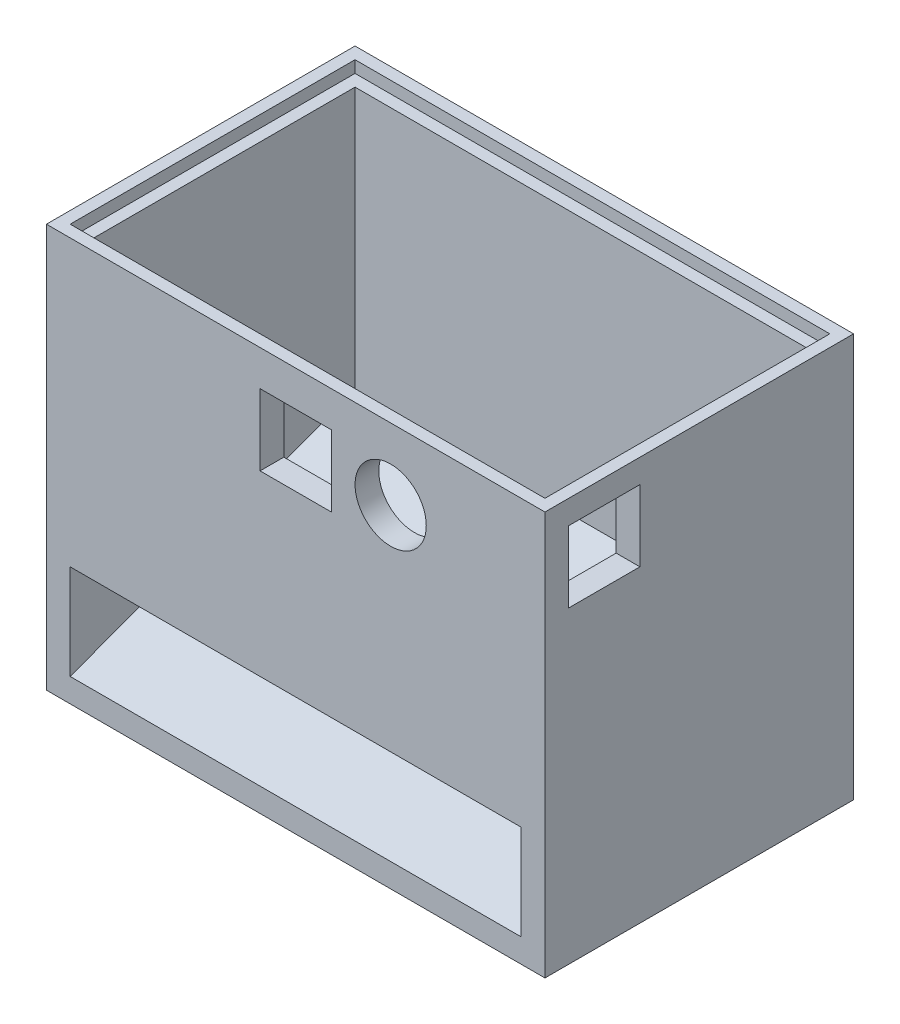
SolidWorks part; units mm, degrees
ref_plane "Front Plane" through (0, 0, 0) normal (0, 0, 1) x (1, 0, 0)
ref_plane "Top Plane" through (0, 0, 0) normal (0, 1, 0) x (1, 0, 0)
ref_plane "Right Plane" through (0, 0, 0) normal (1, 0, 0) x (0, 0, -1)
sketch "Sketch1" plane through (0, 0, 0) normal (0, 1, 0) x (1, 0, 0)
  line L1 (-52.5, -32.5) -> (52.5, -32.5)
  line L2 (-52.5, -32.5) -> (-52.5, 32.5)
  line L3 (-52.5, 32.5) -> (52.5, 32.5)
  line L4 (52.5, -32.5) -> (52.5, 32.5)
  line L5 (-52.5, -32.5) -> (52.5, 32.5) construction
  line L6 (-52.5, 32.5) -> (52.5, -32.5) construction
  point P0 (0, 0)
  dimension "D1" = 105
  dimension "D2" = 65
extrude "Boss-Extrude1" add sketch "Sketch1" along normal blind 5
sketch "Sketch2" plane through (0, 5, 0) normal (0, 1, 0) x (1, 0, 0)
  line L0 (-47.5, -32.5) -> (-47.5, 27.5)
  line L1 (-52.5, -32.5) -> (52.5, -32.5) construction
  line L2 (-47.5, 27.5) -> (47.5, 27.5)
  line L3 (47.5, 27.5) -> (47.5, -32.5)
  line L4 (47.5, -32.5) -> (52.5, -32.5)
  line L5 (52.5, -32.5) -> (52.5, 32.5)
  line L6 (52.5, 32.5) -> (-52.5, 32.5)
  line L7 (-52.5, 32.5) -> (-52.5, -32.5)
  line L8 (-52.5, -32.5) -> (-47.5, -32.5)
  dimension "D1" = 5
  dimension "D2" = 5
  dimension "D3" = 5
extrude "Boss-Extrude2" add sketch "Sketch2" along normal blind 20
sketch "Sketch3" plane through (0, 25, 0) normal (0, 1, 0) x (1, 0, 0)
  line L0 (47.5, 27.5) -> (47.5, -32.5) construction
  line L1 (-52.5, -32.5) -> (52.5, -32.5)
  line L2 (-52.5, -32.5) -> (-52.5, 32.5)
  line L3 (-52.5, 32.5) -> (52.5, 32.5)
  line L4 (52.5, -32.5) -> (52.5, 32.5)
  line L5 (-52.5, -32.5) -> (52.5, 32.5) construction
  line L6 (-52.5, 32.5) -> (52.5, -32.5) construction
  line L7 (-47.5, -27.5) -> (47.5, -27.5)
  line L8 (-47.5, -27.5) -> (-47.5, 27.5)
  line L9 (-47.5, 27.5) -> (47.5, 27.5)
  line L10 (47.5, -27.5) -> (47.5, 27.5)
  line L11 (-47.5, -27.5) -> (47.5, 27.5) construction
  line L12 (-47.5, 27.5) -> (47.5, -27.5) construction
  line L13 (-47.5, 27.5) -> (47.5, 27.5) construction
  point P0 (0, 0)
  point P7 (0, 0)
extrude "Boss-Extrude3" add sketch "Sketch3" along normal blind 60
sketch "Sketch4" plane through (0, 85, 0) normal (0, 1, 0) x (1, 0, 0)
  line L0 (52.5, 32.5) -> (-52.5, 32.5) construction
  line L1 (50, -30) -> (-50, -30)
  line L2 (50, -30) -> (50, 30)
  line L3 (50, 30) -> (-50, 30)
  line L4 (-50, -30) -> (-50, 30)
  line L5 (50, -30) -> (-50, 30) construction
  line L6 (50, 30) -> (-50, -30) construction
  line L7 (-52.5, 32.5) -> (-52.5, -32.5) construction
  point P0 (0, 0)
  dimension "D1" = 2.5
  dimension "D2" = 2.5
extrude "Cut-Extrude1" cut sketch "Sketch4" against normal blind 2.5
sketch "Sketch5" plane through (0, 0, 32.5) normal (0, 0, 1) x (1, 0, 0)
  line L0 (-52.5, 85) -> (-52.5, 0) construction
  line L1 (-35, 77.5) -> (35, 77.5)
  line L2 (-35, 77.5) -> (-35, 27.5)
  line L3 (-35, 27.5) -> (35, 27.5)
  line L4 (35, 77.5) -> (35, 27.5)
  line L5 (-52.5, 85) -> (52.5, 85) construction
  line L7 (-7.5, 77.5) -> (7.5, 77.5)
  line L8 (-7.5, 77.5) -> (-7.5, 62.5)
  line L9 (-7.5, 62.5) -> (7.5, 62.5)
  line L10 (7.5, 77.5) -> (7.5, 62.5)
  line L11 (12.5, 77.5) -> (27.5, 77.5)
  circle A0 centre (20, 70) radius 7.5
  dimension "D1" = 70
  dimension "D2" = 50
  dimension "D3" = 17.5
  dimension "D4" = 7.5
  dimension "D5" = 15
  dimension "D6" = 15
  dimension "D7" = 12.5
  dimension "D9" = 27.5
extrude "Cut-Extrude3" cut sketch "Sketch5" against normal blind 10 contours L10 L1 L8 L9 | A0
sketch "Sketch6" plane through (52.5, 0, 0) normal (1, 0, 0) x (0, 0, -1)
  line L0 (-32.5, 85) -> (-32.5, 0) construction
  line L1 (-27.5, 80) -> (-12.5, 80)
  line L2 (-27.5, 80) -> (-27.5, 65)
  line L3 (-27.5, 65) -> (-12.5, 65)
  line L4 (-12.5, 80) -> (-12.5, 65)
  line L5 (-32.5, 85) -> (32.5, 85) construction
  dimension "D1" = 5
  dimension "D2" = 5
  dimension "D3" = 15
  dimension "D4" = 15
extrude "Cut-Extrude4" cut sketch "Sketch6" against normal blind 10
sketch "Sketch10" plane through (-47.5, 0, 0) normal (1, 0, 0) x (0, 0, -1)
  line L0 (-32.5, 5) -> (27.5, 27.2673)
  line L1 (27.5, 82.5) -> (27.5, 5) construction
  line L2 (27.5, 27.2673) -> (27.5, 5)
  line L3 (27.5, 5) -> (-32.5, 5)
  point P5 (27.5, 27.2673)
extrude "Boss-Extrude4" add sketch "Sketch10" along normal blind 95
